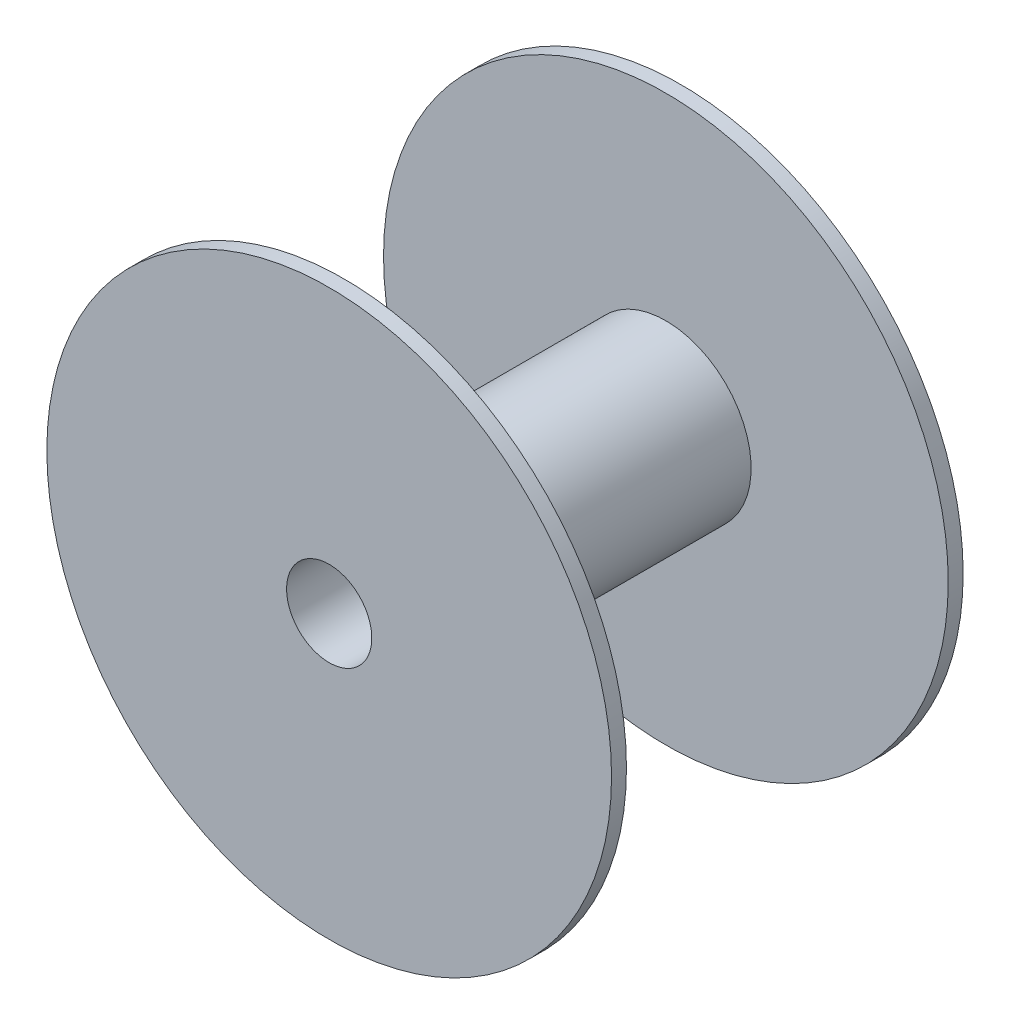
SolidWorks part; units mm, degrees
ref_plane "Спереди" through (0, 0, 0) normal (0, 0, 1) x (1, 0, 0)
ref_plane "Сверху" through (0, 0, 0) normal (0, 1, 0) x (1, 0, 0)
ref_plane "Справа" through (0, 0, 0) normal (1, 0, 0) x (0, 0, -1)
sketch "Эскиз1" plane through (0, 0, 0) normal (0, 0, 1) x (1, 0, 0)
  circle A0 centre (0, 0) radius 80
  dimension "D1" = 160
extrude "Бобышка-Вытянуть1" add sketch "Эскиз1" along normal blind 302
sketch "Эскиз2" plane through (0, 0, 0) normal (0, 0, -1) x (-1, 0, 0)
  circle A0 centre (0, 0) radius 265
  dimension "D1" = 530
extrude "Бобышка-Вытянуть2" add sketch "Эскиз2" along normal blind 14
sketch "Эскиз3" plane through (0, 0, 302) normal (0, 0, 1) x (1, 0, 0)
  circle A0 centre (0, 0) radius 265
  dimension "D1" = 530
extrude "Бобышка-Вытянуть3" add sketch "Эскиз3" along normal blind 14
sketch "Эскиз4" plane through (0, 0, -14) normal (0, 0, -1) x (-1, 0, 0)
  circle A0 centre (0, 0) radius 40
  dimension "D1" = 80
extrude "Вырез-Вытянуть1" cut sketch "Эскиз4" against normal through all
